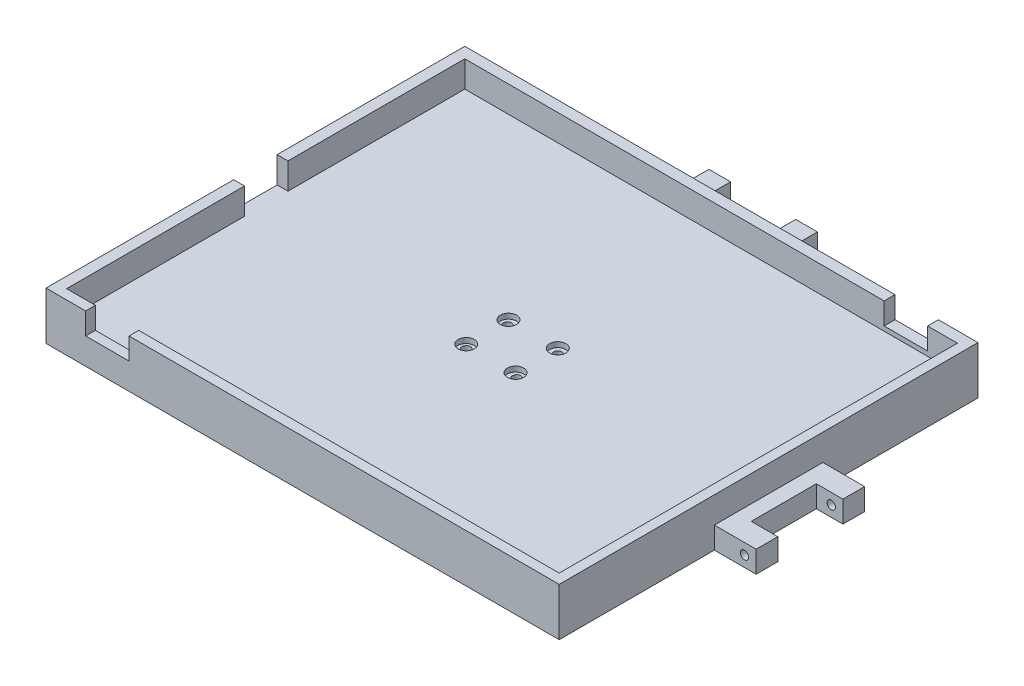
SolidWorks part; units mm, degrees
ref_plane "Front Plane" through (0, 0, 0) normal (0, 0, 1) x (1, 0, 0)
ref_plane "Top Plane" through (0, 0, 0) normal (0, 1, 0) x (1, 0, 0)
ref_plane "Right Plane" through (0, 0, 0) normal (1, 0, 0) x (0, 0, -1)
sketch "Sketch2" plane through (0, 0, 0) normal (0, 1, 0) x (1, 0, 0)
  line L1 (0, 0) -> (227, 0)
  line L2 (0, 0) -> (0, -183.5)
  line L3 (0, -183.5) -> (227, -183.5)
  line L4 (227, 0) -> (227, -183.5)
  line L5 (-5, 5) -> (231.5, 5)
  line L6 (-5, 5) -> (-5, -188)
  line L7 (-5, -188) -> (231.5, -188)
  line L8 (231.5, 5) -> (231.5, -188)
  dimension "D1" = 227
  dimension "D2" = 183.5
  dimension "D3" = 236.5
  dimension "D4" = 5
  dimension "D5" = 193
  dimension "D6" = 5
extrude "Boss-Extrude1" add sketch "Sketch2" along normal blind 12.1
sketch "Sketch3" plane through (0, 0, 0) normal (0, -1, 0) x (1, 0, 0)
  line L1 (-5, 188) -> (231.5, 188)
  line L2 (-5, 188) -> (-5, -5)
  line L3 (-5, -5) -> (231.5, -5)
  line L4 (231.5, 188) -> (231.5, -5)
extrude "Boss-Extrude2" add sketch "Sketch3" along normal blind 10
sketch "Sketch4" plane through (-5, 0, 0) normal (-1, 0, 0) x (0, 0, 1)
  line L0 (-5, 12.1) -> (188, 12.1) construction
  line L1 (81.5, 12.1) -> (101.5, 12.1)
  line L2 (81.5, 12.1) -> (81.5, 2.1)
  line L3 (81.5, 2.1) -> (101.5, 2.1)
  line L4 (101.5, 12.1) -> (101.5, 2.1)
  line L5 (91.5, -10) -> (91.5, 12.1)
  line L6 (188, -10) -> (-5, -10) construction
  line M4 (188, 12.1) -> (-5, 12.1)
  dimension "D1" = 10
  dimension "D2" = 20
  dimension "D3" = 10
extrude "Cut-Extrude1" cut sketch "Sketch4" against normal blind 5 contours L5 L3 L4 M4 | L3 L5 L1 L2
sketch "Sketch7" plane through (0, 0, 188) normal (0, 0, 1) x (1, 0, 0)
  line L0 (113.25, 12.1) -> (113.25, -10) construction
  line L1 (-5, 12.1) -> (231.5, 12.1) construction
  line L2 (231.5, -10) -> (-5, -10) construction
  line L4 (13.25, 12.1) -> (33.25, 12.1)
  line L5 (13.25, 12.1) -> (13.25, 2.1)
  line L6 (13.25, 2.1) -> (33.25, 2.1)
  line L7 (33.25, 12.1) -> (33.25, 2.1)
  dimension "D1" = 20
  dimension "D2" = 100
  dimension "D3" = 10
extrude "Cut-Extrude2" cut sketch "Sketch7" against normal blind 5
sketch "Sketch8" plane through (0, 0, -5) normal (0, 0, -1) x (-1, 0, 0)
  line L0 (-113.25, 12.1) -> (-113.25, -10) construction
  line L1 (-231.5, 12.1) -> (5, 12.1) construction
  line L2 (5, -10) -> (-231.5, -10) construction
  line L4 (-213.25, 12.1) -> (-193.25, 12.1)
  line L5 (-213.25, 12.1) -> (-213.25, 2.1)
  line L6 (-213.25, 2.1) -> (-193.25, 2.1)
  line L7 (-193.25, 12.1) -> (-193.25, 2.1)
  dimension "D1" = 10
  dimension "20" = 20
  dimension "D2" = 200
extrude "Cut-Extrude3" cut sketch "Sketch8" against normal blind 5
sketch "Sketch11" plane through (0, 0, -5) normal (0, 0, -1) x (-1, 0, 0)
  line L0 (-202.0531, 2.1) -> (-202.0531, -10)
  line L1 (-213.25, 2.1) -> (-193.25, 2.1) construction
  line L2 (5, -10) -> (-231.5, -10) construction
sketch "Sketch14" plane through (231.5, 0, 0) normal (1, 0, 0) x (0, 0, -1)
  line L0 (5, -10) -> (-188, -10) construction
  line L1 (-116.5, -10) -> (-66.5, -10)
  line L2 (-116.5, -10) -> (-116.5, 0)
  line L3 (-116.5, 0) -> (-66.5, 0)
  line L4 (-66.5, -10) -> (-66.5, 0)
  line L5 (-91.5, 12.1) -> (-91.5, -10)
  line L6 (-188, 12.1) -> (5, 12.1) construction
  line M2 (-188, -10) -> (5, -10)
  dimension "D1" = 50
  dimension "D2" = 25
  dimension "D3" = 10
extrude "Boss-Extrude6" add sketch "Sketch14" along normal blind 19.25 contours L5 L3 L2 M2 | L3 L5 L1 L4
sketch "Sketch18" plane through (0, 0, 0) normal (0, 1, 0) x (1, 0, 0)
  line L0 (250.75, -116.5) -> (250.75, -66.5) construction
  line L1 (250.75, -76.5) -> (238.5, -76.5)
  line L2 (250.75, -76.5) -> (250.75, -106.5)
  line L3 (250.75, -106.5) -> (238.5, -106.5)
  line L4 (238.5, -76.5) -> (238.5, -106.5)
  line L5 (250.75, -116.5) -> (231.5, -116.5) construction
  line L6 (250.75, -66.5) -> (231.5, -66.5) construction
  point P6 (244.625, -106.5)
  dimension "D1" = 12.25
  dimension "D2" = 10
  dimension "D3" = 10
extrude "Cut-Extrude7" cut sketch "Sketch18" against normal through all
sketch "Sketch19" plane through (0, 0, 116.5) normal (0, 0, 1) x (1, 0, 0)
  circle A0 centre (245.379, -5) radius 1.925
  point P2 (245.9079, -7.5352)
  point P3 (245.379, -5)
  dimension "D1" = 3.85
extrude "Cut-Extrude8" cut sketch "Sketch19" against normal through all
sketch "Sketch21" plane through (0, -10, 0) normal (0, -1, 0) x (1, 0, 0)
  circle A0 centre (124.8714, 82.0162) radius 1.925
  circle A1 centre (124.8714, 100.9838) radius 1.925
  circle A2 centre (101.6286, 100.9838) radius 1.925
  circle A3 centre (101.6286, 82.0162) radius 1.925
  point P4 (124.8714, 82.0162)
  dimension "D2" = 3.85
extrude "Cut-Extrude9" cut sketch "Sketch21" against normal through all
sketch "Sketch22" plane through (0, 0, 0) normal (0, 1, 0) x (1, 0, 0)
  line L0 (113.5, 0) -> (113.5, -139.4789)
  line L1 (227, 0) -> (0, 0) construction
  line L2 (0, -91.75) -> (187.9624, -91.75)
  line L3 (0, 0) -> (0, -183.5) construction
  circle A0 centre (124.8714, -82.0162) radius 3.75
  circle A1 centre (124.8714, -101.4838) radius 3.75
  circle A2 centre (102.1286, -101.4838) radius 3.75
  circle A3 centre (102.1286, -82.0162) radius 3.75
  circle M6 centre (101.6286, -82.0162) radius 1.925
  circle M7 centre (101.6286, -100.9838) radius 1.925
  circle M8 centre (124.8714, -100.9838) radius 1.925
  circle M9 centre (124.8714, -82.0162) radius 1.925
  dimension "D1" = 7.5
extrude "Cut-Extrude10" cut sketch "Sketch22" against normal blind 2.4 contours A3 M6 | A0 M9 | A1 M8 | A2 M7
sketch "Sketch26" plane through (0, 0, 66.5) normal (0, 0, -1) x (-1, 0, 0)
  circle A0 centre (-236.9045, -5) radius 2.0482
sketch "Sketch27" plane through (0, 0, -5) normal (0, 0, -1) x (-1, 0, 0)
  line L0 (-113.25, -10) -> (-113.25, 12.1)
  line L1 (5, -10) -> (-231.5, -10) construction
  line L2 (-193.25, 12.1) -> (5, 12.1) construction
  line L4 (-138.25, -10) -> (-88.25, -10)
  line L5 (-138.25, -10) -> (-138.25, 0)
  line L6 (-138.25, 0) -> (-88.25, 0)
  line L7 (-88.25, -10) -> (-88.25, 0)
  line M9 (-231.5, -10) -> (5, -10)
  dimension "D1" = 50
  dimension "D2" = 10
  dimension "D3" = 25
extrude "Boss-Extrude7" add sketch "Sketch27" along normal blind 19.25 contours L6 L5 L0 M9 | L7 L6 L0 M9
sketch "Sketch28" plane through (0, 0, 0) normal (0, 1, 0) x (1, 0, 0)
  line L0 (138.25, 24.25) -> (88.25, 24.25) construction
  line L1 (98.25, 24.25) -> (128.25, 24.25)
  line L2 (98.25, 24.25) -> (98.25, 12.25)
  line L3 (98.25, 12.25) -> (128.25, 12.25)
  line L4 (128.25, 24.25) -> (128.25, 12.25)
  line L5 (138.25, 24.25) -> (138.25, 5) construction
  line L6 (88.25, 24.25) -> (88.25, 5) construction
  dimension "D1" = 10
  dimension "D2" = 10
  dimension "D3" = 12
extrude "Cut-Extrude11" cut sketch "Sketch28" against normal blind 19.25
sketch "Sketch30" plane through (0, 0, 116.5) normal (0, 0, 1) x (1, 0, 0)
  point P0 (245.379, -5)
sketch "Sketch31" plane through (138.25, 0, 0) normal (1, 0, 0) x (0, 0, -1)
  line L0 (24.25, -10) -> (24.25, 0) construction
  circle A0 centre (18.88, -5) radius 1.925
  point P0 (18.88, -5)
  dimension "D2" = 3.85
  dimension "D1" = 5.37
extrude "Cut-Extrude12" cut sketch "Sketch31" against normal through all
sketch "Sketch32" plane through (0, 0, 0) normal (1, 0, 0) x (0, 0, -1)
  line L0 (0, 0) -> (-183.5, 0) construction
  line L1 (-101.5, 12.1) -> (-81.5, 12.1)
  line L2 (-101.5, 12.1) -> (-101.5, 0)
  line L3 (-101.5, 0) -> (-81.5, 0)
  line L4 (-81.5, 12.1) -> (-81.5, 0)
extrude "Cut-Extrude14" cut sketch "Sketch32" against normal through all
